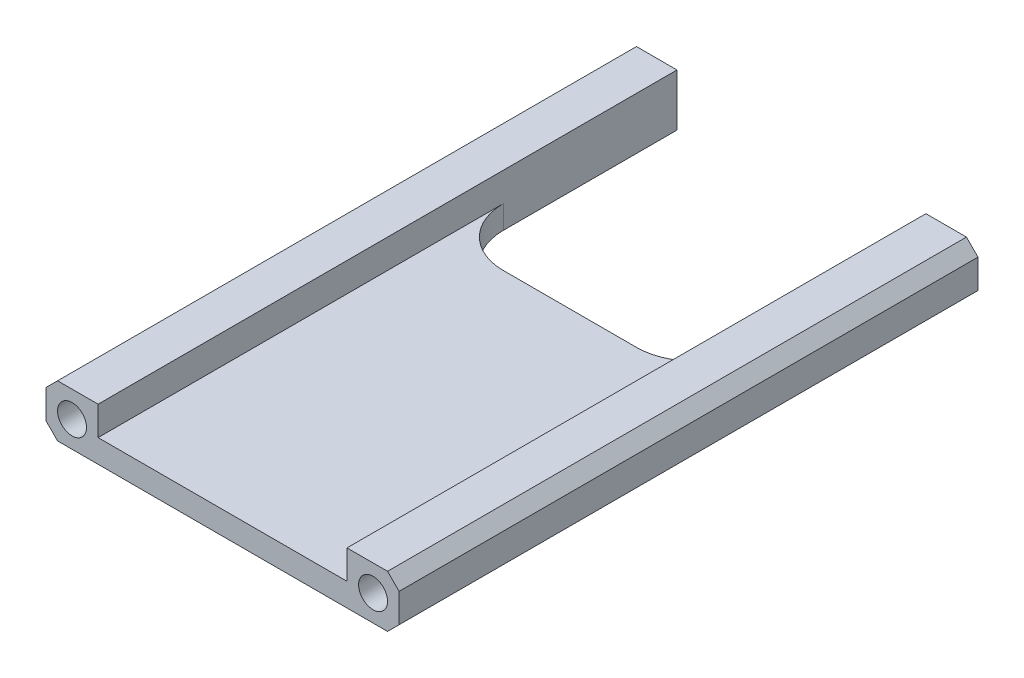
SolidWorks part; units mm, degrees
ref_plane "Front Plane" through (0, 0, 0) normal (0, 0, 1) x (1, 0, 0)
ref_plane "Top Plane" through (0, 0, 0) normal (0, 1, 0) x (1, 0, 0)
ref_plane "Right Plane" through (0, 0, 0) normal (1, 0, 0) x (0, 0, -1)
sketch "Sketch1" plane through (0, 0, 0) normal (0, 1, 0) x (1, 0, 0)
  line L1 (0, 0) -> (77.47, 0)
  line L2 (0, 0) -> (0, 127)
  line L3 (0, 127) -> (77.47, 127)
  line L4 (77.47, 0) -> (77.47, 127)
  dimension "D1" = 77.47
  dimension "D2" = 127
extrude "Boss-Extrude1" add sketch "Sketch1" along normal blind 11.43
sketch "Sketch2" plane through (0, 0, 0) normal (0, 0, 1) x (1, 0, 0)
  line L0 (5.715, 5.715) -> (71.755, 5.715) construction
  line L1 (38.735, 11.43) -> (38.735, 0) construction
  line L2 (0, 11.43) -> (77.47, 11.43) construction
  line L3 (0, 0) -> (77.47, 0) construction
  circle A0 centre (5.715, 5.715) radius 3.175
  circle A1 centre (71.755, 5.715) radius 3.175
  point P10 (38.735, 5.715)
  dimension "D1" = 6.35
  dimension "D2" = 66.04
extrude "Cut-Extrude1" cut sketch "Sketch2" against normal through all
sketch "Sketch3" plane through (0, 11.43, 0) normal (0, 1, 0) x (1, 0, 0)
  line L0 (11.43, 127) -> (11.43, 88.9)
  line L1 (77.47, 127) -> (0, 127) construction
  line L2 (11.43, 127) -> (66.04, 127)
  line L3 (66.04, 127) -> (66.04, 88.9)
  line L4 (53.34, 76.2) -> (24.13, 76.2)
  line L5 (0, 127) -> (0, 0) construction
  arc A0 (66.04, 88.9) -> (53.34, 76.2) centre (53.34, 88.9) cw
  arc A1 (24.13, 76.2) -> (11.43, 88.9) centre (24.13, 88.9) cw
  point P10 (38.735, 127)
  dimension "D1" = 12.7
  dimension "D2" = 11.43
  dimension "D3" = 50.8
extrude "Cut-Extrude2" cut sketch "Sketch3" against normal through all
sketch "Sketch4" plane through (0, 0, -127) normal (0, 0, -1) x (-1, 0, 0)
  line L0 (-11.43, 0) -> (-11.43, 11.43) construction
  line L1 (-66.04, 11.43) -> (-11.43, 11.43)
  line L2 (-66.04, 11.43) -> (-66.04, 5.08)
  line L3 (-66.04, 5.08) -> (-11.43, 5.08)
  line L4 (-11.43, 11.43) -> (-11.43, 5.08)
  line L5 (-11.43, 0) -> (0, 0) construction
  dimension "D1" = 5.08
extrude "Cut-Extrude3" cut sketch "Sketch4" against normal through all
chamfer "Chamfer1" distance 2.54 angle 45 4 edges at (0, 0, -63.5) (0, 11.43, -63.5) (77.47, 0, -63.5) (77.47, 11.43, -63.5)
